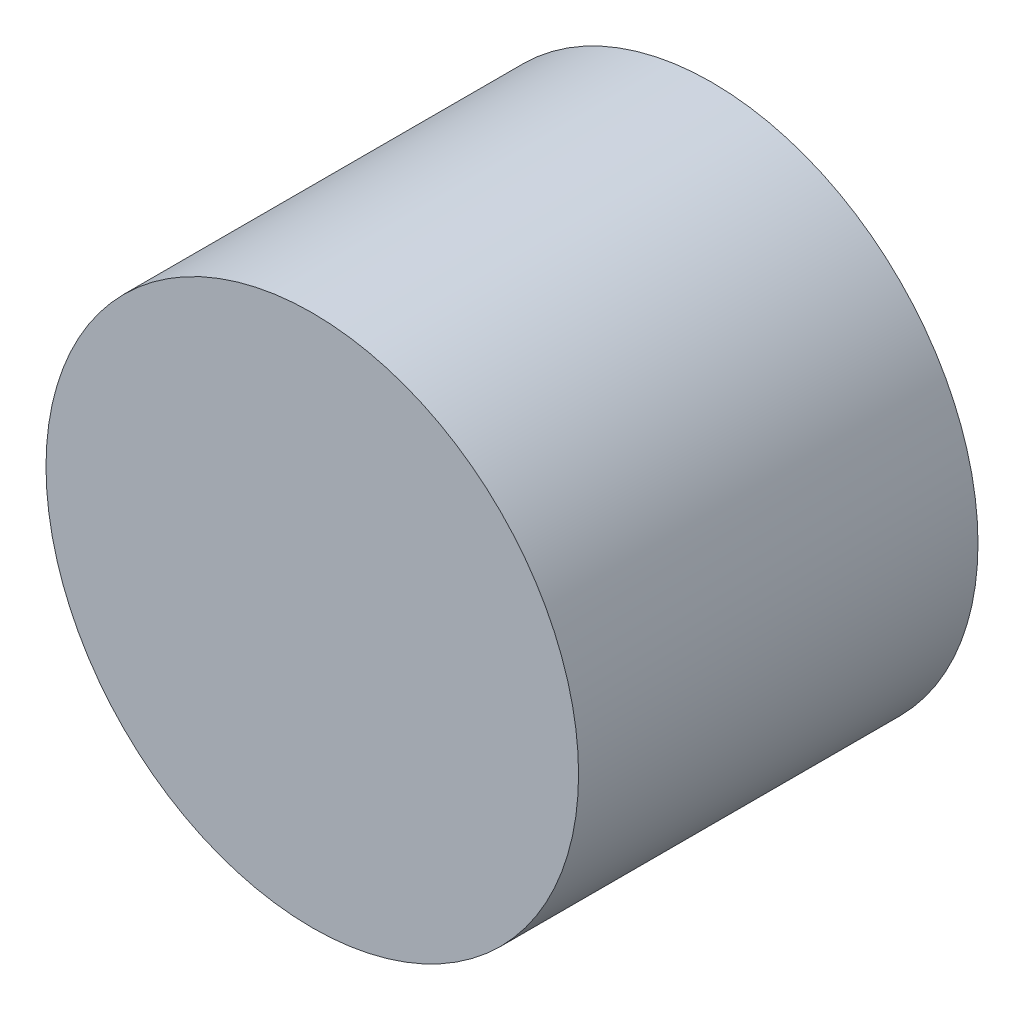
SolidWorks part; units mm, degrees
ref_plane "Front Plane" through (0, 0, 0) normal (0, 0, 1) x (1, 0, 0)
ref_plane "Top Plane" through (0, 0, 0) normal (0, 1, 0) x (1, 0, 0)
ref_plane "Right Plane" through (0, 0, 0) normal (1, 0, 0) x (0, 0, -1)
sketch "Sketch1" plane through (0, 0, 0) normal (0, 0, 1) x (1, 0, 0)
  circle A0 centre (0, 0) radius 6
  dimension "D1" = 12
extrude "Boss-Extrude1" add sketch "Sketch1" along normal blind 9
